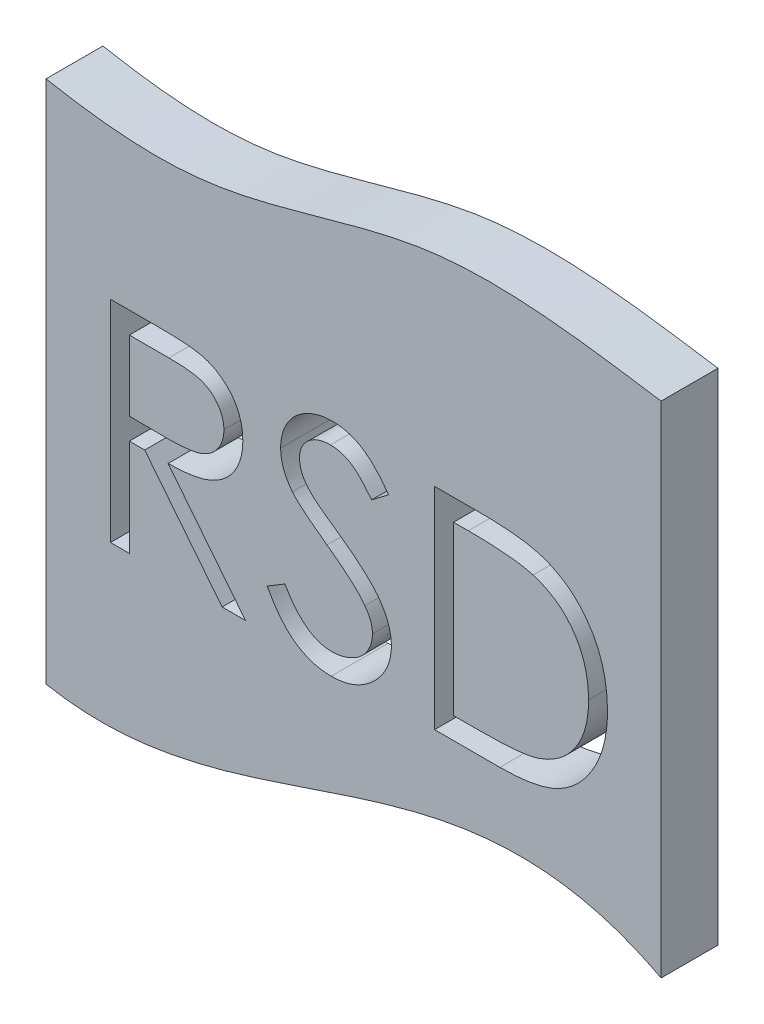
SolidWorks part; units mm, degrees
ref_plane "Front Plane" through (0, 0, 0) normal (0, 0, 1) x (1, 0, 0)
ref_plane "Top Plane" through (0, 0, 0) normal (0, 1, 0) x (1, 0, 0)
ref_plane "Right Plane" through (0, 0, 0) normal (1, 0, 0) x (0, 0, -1)
sketch "Sketch4" plane through (0, 0, 0) normal (0, 0, 1) x (1, 0, 0)
  line L5 (286.7718, -236.3727) -> (286.7718, 202.7985)
  line L6 (-253.8596, 177.7772) -> (-253.8596, -283.0059)
  spline S0 degree 3 poles (-253.8596, 177.7772) (-207.7006, 169.0188) (-94.6354, 157.8659) (81.2095, 234.4247) (218.105, 213.363) (286.7718, 202.7985) knots 0.162783 0.162783 0.162783 0.162783 0.375756 0.686879 1 1 1 1
  spline S1 degree 3 poles (-253.8596, -283.0059) (-207.1706, -291.8781) (-28.4347, -271.1647) (144.4176, -161.0387) (286.7718, -236.3727) knots 0.159406 0.159406 0.159406 0.159406 0.373982 1 1 1 1
  dimension "D1" = 82.2264
  dimension "D2" = 286.7718
  dimension "D3" = 116.303
  dimension "D4" = 253.8596
  dimension "D5" = 169.7102
  dimension "D6" = 177.7772
  dimension "D7" = 202.7985
  dimension "D8" = 214.8306
  dimension "D9" = 215.3165
  dimension "D10" = 236.3727
  dimension "D11" = 275.4769
  dimension "D12" = 283.0059
extrude "Boss-Extrude2" add sketch "Sketch4" along normal blind 50 contours L6 S1 L5 S0
sketch "Sketch5" plane through (0, 0, 50) normal (0, 0, 1) x (1, 0, 0)
  line L0 (-197.2458, 38.3435) -> (-160.1819, 38.3435)
  line L3 (-146.5658, -61.384) -> (-78.5225, -146.8648)
  line L4 (-78.5225, -146.8648) -> (-99.0765, -146.8648)
  line L5 (-99.0765, -146.8648) -> (-167.1198, -61.384)
  line L6 (-167.1198, -61.384) -> (-180.6245, -61.384)
  line L7 (-180.6245, -61.384) -> (-180.6245, -146.8648)
  line L8 (-180.6245, -146.8648) -> (-197.2458, -146.8648)
  line L9 (-197.2458, -146.8648) -> (-197.2458, 38.3435)
  line L10 (-180.6245, 19.3478) -> (-180.6245, -42.3883)
  line L11 (-180.6245, -42.3883) -> (-146.7142, -42.648)
  line L12 (-145.898, 19.3478) -> (-180.6245, 19.3478)
  line L13 (-59.5268, -111.1365) -> (-43.8701, -101.75)
  line L14 (47.3242, 11.7421) -> (32.2983, 0.3521)
  line L15 (87.6901, -146.8648) -> (87.6901, 38.3435)
  line L16 (87.6901, 38.3435) -> (125.0879, 38.3435)
  line L17 (145.0854, -146.8648) -> (87.6901, -146.8648)
  line L18 (104.3114, -127.8691) -> (125.5702, -127.8691)
  line L19 (117.3338, 19.3478) -> (104.3114, 19.3478)
  line L20 (104.3114, 19.3478) -> (104.3114, -127.8691)
  spline S0 degree 3 poles (-160.1819, 38.3435) (-155.4336, 38.3165) (-148.6271, 38.3316) (-139.9736, 37.9787) (-134.4162, 37.7616) (-129.4841, 37.3638) (-124.1311, 36.9) (-120.4482, 36.3191) (-118.2206, 35.8207) knots 0 0 0 0 0.338434 0.484822 0.617158 0.734698 0.837385 1 1 1 1
  spline S1 degree 3 poles (-118.2206, 35.8207) (-115.5229, 35.2279) (-111.6002, 33.9919) (-106.646, 31.8019) (-103.1643, 29.9002) (-99.8975, 27.6998) (-96.8115, 25.241) (-93.8923, 22.5365) (-91.258, 19.5184) (-88.7742, 16.3521) (-86.6793, 12.9282) (-84.8735, 9.3478) (-83.4354, 5.5744) (-82.2788, 1.6448) (-81.168, -3.9353) (-80.8894, -8.2588) (-80.897, -11.1863) knots 0 0 0 0 0.127064 0.188745 0.249132 0.309453 0.369827 0.43065 0.492352 0.554072 0.61569 0.676798 0.738439 0.801317 0.865185 1 1 1 1
  spline S2 degree 3 poles (-80.897, -11.1863) (-80.8801, -15.9923) (-81.6985, -23.1269) (-84.8597, -31.9765) (-88.0485, -38.0174) (-92.1144, -43.4632) (-96.9997, -48.2463) (-102.7085, -52.2489) (-108.0229, -55.0246) (-112.7173, -56.8022) (-116.582, -58.053) (-120.7977, -59.0193) (-125.3241, -59.8851) (-130.1799, -60.5382) (-137.2877, -61.1988) (-142.7914, -61.3701) (-146.5658, -61.384) knots 0 0 0 0 0.153721 0.226714 0.299191 0.37119 0.443006 0.516689 0.593217 0.633873 0.676989 0.7229 0.771959 0.824211 0.879379 1 1 1 1
  spline S3 degree 3 poles (-146.7142, -42.648) (-143.6446, -42.6973) (-139.2028, -42.5345) (-133.4885, -42.1977) (-129.6763, -41.8307) (-126.1842, -41.3566) (-123.0138, -40.7638) (-120.1599, -40.0732) (-116.8315, -39.0042) (-113.1149, -37.3105) (-109.0756, -34.8464) (-105.6361, -31.7471) (-102.7293, -28.2031) (-100.3969, -24.3065) (-98.1786, -18.6793) (-97.5068, -14.1748) (-97.5182, -11.1492) knots 0 0 0 0 0.138913 0.201185 0.259124 0.312255 0.360682 0.405086 0.445102 0.518778 0.589462 0.658462 0.727283 0.796322 0.863175 1 1 1 1
  spline S4 degree 3 poles (-97.5182, -11.1492) (-97.528, -8.2053) (-98.1405, -3.762) (-100.4794, 1.6909) (-102.8223, 5.5094) (-105.6804, 8.9758) (-109.0308, 11.9416) (-112.7829, 14.389) (-116.2898, 15.9529) (-119.4243, 16.9118) (-122.1458, 17.5865) (-125.2208, 18.1286) (-128.6644, 18.563) (-132.4618, 18.9361) (-138.2497, 19.2867) (-142.7684, 19.3583) (-145.898, 19.3478) knots 0 0 0 0 0.136365 0.204019 0.273064 0.342913 0.410965 0.479169 0.549308 0.587652 0.630647 0.678879 0.731934 0.791111 0.855283 1 1 1 1
  spline S5 degree 3 poles (-43.8701, -101.75) (-41.1589, -106.4566) (-36.8772, -113.057) (-30.1465, -120.5315) (-25.1212, -124.919) (-19.921, -128.367) (-12.7775, -131.6183) (-7.0173, -132.628) (-3.2074, -132.618) knots 0 0 0 0 0.304646 0.438547 0.562322 0.677433 0.786897 1 1 1 1
  spline S6 degree 3 poles (-3.2074, -132.618) (0.0136, -132.6471) (4.813, -132.0811) (10.9778, -130.2961) (15.3492, -128.403) (19.4288, -126.1091) (23.0064, -123.3392) (26.099, -120.238) (28.6294, -116.7781) (30.5687, -113.0573) (32.5618, -107.9744) (33.0285, -103.8991) (33.0774, -101.2305) knots 0 0 0 0 0.18093 0.270088 0.360156 0.448343 0.532666 0.613834 0.693982 0.772716 0.849335 1 1 1 1
  spline S7 degree 3 poles (33.0774, -101.2305) (33.0948, -98.0924) (31.8309, -91.5452) (28.4552, -85.8114) (26.4363, -83.051) knots 0 0 0 0 0.477158 1 1 1 1
  spline S8 degree 3 poles (26.4363, -83.051) (24.7293, -80.7994) (21.8415, -77.385) (17.3607, -73.0294) (13.451, -69.3743) (8.9987, -65.6551) (2.2857, -60.1758) (-3.1832, -56.2363) (-6.9546, -53.5186) knots 0 0 0 0 0.18953 0.299198 0.418926 0.548376 0.688136 1 1 1 1
  spline S9 degree 3 poles (-6.9546, -53.5186) (-10.7024, -50.8959) (-15.9478, -47.0041) (-22.4976, -41.9377) (-26.5855, -38.6415) (-30.098, -35.6469) (-33.7489, -32.3793) (-36.0251, -29.9063) (-37.3033, -28.327) knots 0 0 0 0 0.347082 0.495568 0.628357 0.74552 0.845831 1 1 1 1
  spline S10 degree 3 poles (-37.3033, -28.327) (-38.9409, -26.2068) (-41.2239, -22.9519) (-43.6637, -18.3114) (-45.0808, -14.7932) (-46.2718, -11.2352) (-47.35, -6.3692) (-47.6686, -2.6288) (-47.6545, -0.1302) knots 0 0 0 0 0.262559 0.388264 0.512667 0.633722 0.755394 1 1 1 1
  spline S11 degree 3 poles (-47.6545, -0.1302) (-47.6639, 3.7453) (-46.9328, 9.5107) (-44.4665, 16.7775) (-41.9138, 21.8749) (-38.6186, 26.5298) (-34.8064, 30.7956) (-30.2655, 34.3816) (-25.2832, 37.5154) (-19.83, 39.9658) (-12.1533, 42.4608) (-6.0634, 43.0402) (-2.0202, 43.0925) knots 0 0 0 0 0.16578 0.24628 0.327461 0.408797 0.489715 0.571376 0.655523 0.741019 0.826547 1 1 1 1
  spline S12 degree 3 poles (-2.0202, 43.0925) (2.3146, 43.0994) (8.8238, 42.3023) (17.0339, 39.4094) (21.9785, 36.9683) (25.8485, 34.5268) (28.7998, 32.3033) (31.7904, 29.7434) (34.8448, 26.8406) (37.9103, 23.5674) (42.2036, 18.5974) (45.3075, 14.583) (47.3242, 11.7421) knots 0 0 0 0 0.213252 0.31883 0.426794 0.483646 0.543604 0.608308 0.677127 0.750686 0.828713 1 1 1 1
  spline S13 degree 3 poles (32.2983, 0.3521) (30.5765, 2.6236) (27.9634, 5.8082) (24.4905, 9.8035) (22.0276, 12.3049) (19.7312, 14.5645) (17.5025, 16.4991) (15.3735, 18.1276) (12.6897, 19.8659) (9.318, 21.5868) (3.6398, 23.5525) (-0.8669, 24.0785) (-3.8752, 24.0967) knots 0 0 0 0 0.189629 0.274184 0.352183 0.423199 0.488551 0.548473 0.60144 0.701198 0.799592 1 1 1 1
  spline S14 degree 3 poles (-3.8752, 24.0967) (-7.5567, 24.1495) (-12.9654, 23.3622) (-19.4308, 20.4297) (-23.4826, 17.4528) (-26.8516, 13.9216) (-30.1348, 8.4831) (-31.0277, 3.7667) (-31.0332, 0.6489) knots 0 0 0 0 0.275903 0.402371 0.528414 0.650356 0.765895 1 1 1 1
  spline S15 degree 3 poles (-31.0332, 0.6489) (-31.0966, -1.3448) (-30.6443, -4.3037) (-29.6421, -8.1906) (-28.4622, -11.0972) (-26.829, -14.0333) (-23.7995, -18.3027) (-20.9109, -21.2729) (-18.827, -23.2813) knots 0 0 0 0 0.214746 0.322939 0.434116 0.553412 0.686073 1 1 1 1
  spline S16 degree 3 poles (-18.827, -23.2813) (-17.8751, -24.1536) (-16.1344, -25.5865) (-13.3718, -27.6451) (-10.5433, -29.7936) (-7.1581, -32.2845) (-1.5483, -36.2763) (2.8987, -39.4915) (6.0678, -41.7205) knots 0 0 0 0 0.124952 0.218094 0.333502 0.468789 0.624938 1 1 1 1
  spline S17 degree 3 poles (6.0678, -41.7205) (9.9651, -44.5438) (15.5942, -48.6834) (22.5297, -54.4327) (27.0522, -58.4742) (31.1203, -62.3651) (34.6889, -66.152) (37.7942, -69.8078) (41.1382, -74.4947) (44.549, -80.2512) (48.413, -89.4742) (49.695, -96.7243) (49.6986, -101.4903) knots 0 0 0 0 0.187773 0.272396 0.351321 0.424335 0.491909 0.554233 0.611268 0.716348 0.81454 1 1 1 1
  spline S18 degree 3 poles (49.6986, -101.4903) (49.75, -104.7824) (49.2126, -109.6555) (47.6415, -115.9582) (45.8957, -120.4515) (43.7613, -124.8301) (41.0539, -128.9792) (37.9155, -132.9906) (34.3154, -136.7574) (30.376, -140.2153) (26.2123, -143.2913) (21.8175, -145.856) (17.2156, -147.9493) (12.4054, -149.5845) (5.6273, -151.1957) (0.3462, -151.6275) (-3.2074, -151.6137) knots 0 0 0 0 0.121775 0.18092 0.240256 0.300114 0.361146 0.423501 0.488669 0.553954 0.617581 0.680238 0.742187 0.804663 0.868259 1 1 1 1
  spline S19 degree 3 poles (-3.2074, -151.6137) (-5.9899, -151.6304) (-10.1181, -151.2942) (-15.5276, -150.3841) (-19.423, -149.318) (-23.235, -148.0224) (-26.947, -146.4277) (-30.5607, -144.5164) (-34.0965, -142.3313) (-37.5452, -139.7882) (-40.8747, -136.8263) (-44.1941, -133.5271) (-47.4057, -129.8013) (-50.5733, -125.7085) (-54.7744, -119.5461) (-57.6656, -114.5867) (-59.5268, -111.1365) knots 0 0 0 0 0.113696 0.169178 0.224159 0.27872 0.333794 0.389241 0.445822 0.503704 0.564294 0.627975 0.695038 0.765373 0.839611 1 1 1 1
  spline S20 degree 3 poles (125.0879, 38.3435) (131.3714, 38.3177) (140.4586, 38.1858) (152.1084, 37.4801) (159.8044, 36.7419) (166.8141, 35.8318) (174.8207, 34.397) (180.4157, 32.8833) (183.856, 31.6653) knots 0 0 0 0 0.317406 0.458844 0.589367 0.707831 0.81577 1 1 1 1
  spline S21 degree 3 poles (183.856, 31.6653) (188.127, 30.1498) (194.3117, 27.388) (201.9476, 22.7361) (207.3044, 18.8775) (212.2149, 14.4974) (216.8721, 9.7849) (221.085, 4.5679) (224.9431, -1.0452) (228.4216, -6.9884) (231.4452, -13.2503) (233.9562, -19.7991) (236.0413, -26.6166) (237.6822, -33.7179) (239.2085, -43.718) (239.6835, -51.4023) (239.6559, -56.598) knots 0 0 0 0 0.121694 0.181155 0.239875 0.298702 0.357647 0.417605 0.478494 0.540407 0.602345 0.665004 0.728559 0.793651 0.860534 1 1 1 1
  spline S22 degree 3 poles (239.6559, -56.598) (239.6744, -61.1108) (239.2765, -67.7768) (238.1108, -76.4982) (236.7872, -82.7215) (235.178, -88.7714) (233.1162, -94.5833) (230.7542, -100.2107) (227.9999, -105.5774) (224.9762, -110.6618) (221.7313, -115.4547) (218.2686, -119.8878) (214.5551, -123.9745) (210.6389, -127.7086) (206.4942, -131.1213) (202.1104, -134.1458) (197.5072, -136.9011) (192.5501, -139.3045) (187.1455, -141.3382) (181.2701, -143.0233) (174.9384, -144.4296) (168.1394, -145.5438) (158.1465, -146.5777) (150.3974, -146.8926) (145.0854, -146.8648) knots 0 0 0 0 0.090807 0.134295 0.177024 0.218823 0.260244 0.30108 0.341614 0.381583 0.42012 0.458075 0.494738 0.531195 0.566934 0.602713 0.638327 0.674853 0.713467 0.754442 0.797815 0.843989 0.893072 1 1 1 1
  spline S23 degree 3 poles (125.5702, -127.8691) (131.4453, -127.8662) (139.8975, -127.7541) (150.6685, -127.2466) (157.6601, -126.741) (163.9189, -126.0683) (170.8478, -125.1428) (175.6259, -124.0671) (178.5134, -123.1573) knots 0 0 0 0 0.330628 0.475549 0.606746 0.725024 0.829742 1 1 1 1
  spline S24 degree 3 poles (178.5134, -123.1573) (181.8621, -122.0216) (186.794, -120.1272) (192.8389, -116.6963) (197.0782, -113.8712) (201.0113, -110.6618) (204.685, -107.1391) (208.0919, -103.2849) (211.1967, -99.1041) (213.9753, -94.6226) (216.3815, -89.8845) (218.4902, -84.9417) (220.1457, -79.7184) (221.4417, -74.2611) (222.6949, -66.5405) (223.0362, -60.5896) (223.0347, -56.5609) knots 0 0 0 0 0.123338 0.183125 0.241783 0.300579 0.35968 0.418882 0.479531 0.540851 0.602303 0.664463 0.727806 0.792895 0.859672 1 1 1 1
  spline S25 degree 3 poles (223.0347, -56.5609) (223.0836, -52.3044) (222.641, -46.0339) (221.3018, -37.8909) (219.8864, -32.1241) (218.0799, -26.5844) (215.826, -21.3023) (213.2507, -16.222) (210.1867, -11.4609) (206.8309, -6.958) (203.1068, -2.8329) (199.0733, 0.9238) (194.7747, 4.3711) (190.0894, 7.3684) (183.3906, 10.9966) (177.9538, 13.0009) (174.2468, 14.1537) knots 0 0 0 0 0.137813 0.203226 0.267174 0.330024 0.391794 0.453084 0.514334 0.575 0.634865 0.694116 0.753442 0.813126 0.87408 1 1 1 1
  spline S26 degree 3 poles (174.2468, 14.1537) (170.965, 15.1462) (165.5985, 16.27) (157.9366, 17.3692) (151.1693, 18.1158) (143.7058, 18.6482) (132.3545, 19.2092) (123.4816, 19.3683) (117.3338, 19.3478) knots 0 0 0 0 0.179285 0.286583 0.405111 0.535593 0.67819 1 1 1 1
extrude "Cut-Extrude3" cut sketch "Sketch5" against normal blind 50
